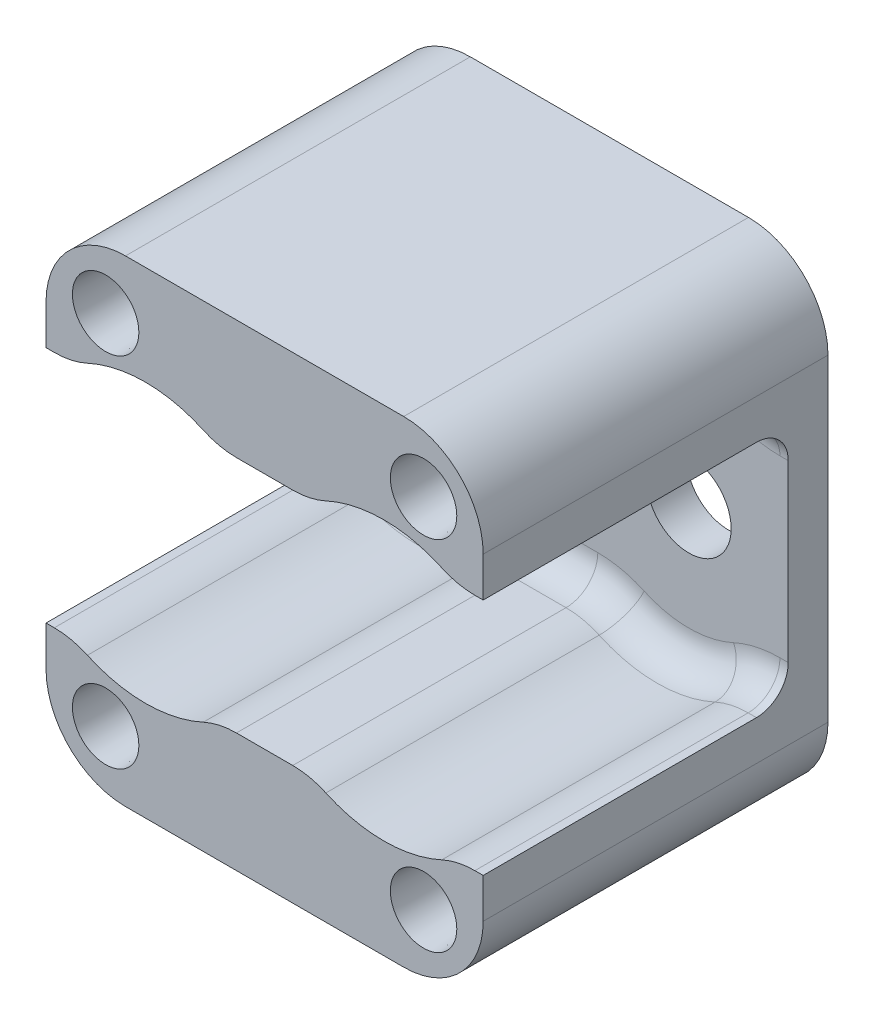
SolidWorks part; units mm, degrees
material "PET"
ref_plane "Front Plane" through (0, 0, 0) normal (0, 0, 1) x (1, 0, 0)
ref_plane "Top Plane" through (0, 0, 0) normal (0, 1, 0) x (1, 0, 0)
ref_plane "Right Plane" through (0, 0, 0) normal (1, 0, 0) x (0, 0, -1)
sketch "Sketch1" plane through (0, 0, 0) normal (0, 0, 1) x (1, 0, 0)
  line L0 (-19.05, 0) -> (0, 0) construction
  line L2 (7.9375, -19.05) -> (-26.9875, -19.05)
  line L3 (7.9375, -19.05) -> (7.9375, 19.05)
  line L4 (7.9375, 19.05) -> (-26.9875, 19.05)
  line L5 (-26.9875, -19.05) -> (-26.9875, 19.05)
  line L6 (7.9375, -19.05) -> (-26.9875, 19.05) construction
  line L7 (7.9375, 19.05) -> (-26.9875, -19.05) construction
  point P4 (-9.525, 0)
  dimension "D1" = 34.925
  dimension "D2" = 38.1
extrude "Boss-Extrude1" add sketch "Sketch1" along normal blind 3.175
sketch "Sketch2" plane through (0, 0, 3.175) normal (0, 0, 1) x (1, 0, 0)
  line L0 (7.9375, -19.05) -> (7.9375, 19.05) construction
  line L1 (-26.9875, 19.05) -> (7.9375, 19.05)
  line L2 (-26.9875, 19.05) -> (-26.9875, 9.525)
  line L3 (-26.9875, 9.525) -> (7.9375, 9.525)
  line L4 (7.9375, 19.05) -> (7.9375, 9.525)
  dimension "D1" = 9.525
extrude "Boss-Extrude2" add sketch "Sketch2" along normal up to surface (24.3713 mm away)
sketch "Sketch3" plane through (0, 0, 19.6088) normal (0, 0, 1) x (1, 0, 0)
  circle A0 centre (-19.05, 0) radius 11.1125
  circle A1 centre (0, 0) radius 11.1125
  dimension "D1" = 22.225
extrude "Cut-Extrude1" cut sketch "Sketch3" against normal up to surface (16.4338 mm away) and the other way through all contours A1 A0 | A0 A1 | A0 A1 up to face at (-13.8906, -4.7625, 3.175)
mirror "Mirror1" about plane through (0, 0, 0) normal (0, 1, 0) of "Cut-Extrude1", "Boss-Extrude2"
fillet "Fillet1" radius 6.35 12 edges at (7.9375, 19.05, 13.7732) (-26.9875, 19.05, 13.7732) (5.7238, 9.525, 15.3607) (-5.7238, 9.525, 15.3607) (-13.3262, 9.525, 15.3607) (-24.7738, 9.525, 15.3607) (7.9375, -19.05, 13.7732) (-26.9875, -19.05, 13.7732) (5.7238, -9.525, 15.3607) (-5.7238, -9.525, 15.3607) (-13.3262, -9.525, 15.3607) (-24.7738, -9.525, 15.3607)
fillet "Fillet2" radius 2.54 18 edges at (5.921, 9.671, 3.175) (0, 11.1125, 3.175) (-5.921, 9.671, 3.175) (-13.129, 9.671, 3.175) (-19.05, 11.1125, 3.175) (-24.971, 9.671, 3.175) (7.6062, -9.525, 3.175) (5.921, -9.671, 3.175) (0, -11.1125, 3.175) (-5.921, -9.671, 3.175) (-9.525, -9.525, 3.175) (-13.129, -9.671, 3.175) (-19.05, -11.1125, 3.175) (-24.971, -9.671, 3.175) (-26.6562, -9.525, 3.175)
sketch "Sketch4" plane through (0, 0, 3.175) normal (0, 0, 1) x (1, 0, 0)
  line L0 (-19.05, 0) -> (-23.3706, 1.7896) construction
  line L1 (-22.5585, -3.2205) -> (-18.8463, -4.7581) construction
  line L2 (-19.8994, 4.7507) -> (-15.0902, 2.7586)
  line L3 (-15.5415, 3.2205) -> (-19.2537, 4.7581) construction
  line L4 (-19.05, 0) -> (-20.8968, -4.4586) construction
  arc A0 (-20.8968, -4.4586) -> (-15.0902, 2.7586) centre (-19.05, 0) ccw
  arc A1 (-19.8994, 4.7507) -> (-20.8968, -4.4586) centre (-19.05, 0) ccw
  dimension "D1" = 9.652
  dimension "D2" = 8.89
extrude "Cut-Extrude2" cut sketch "Sketch4" against normal through all
hole_wizard "1/4 Clearance Hole1" positions "Sketch6" profile "Sketch5" hole size "1/4" standard "ANSI Inch" end condition through all
sketch "Sketch6" plane through (0, 0, 3.175) normal (0, 0, 1) x (1, 0, 0)
  point P0 (0, 0)
sketch "Sketch5" plane through (0, 0, 3.175) normal (1, 0, 0) x (0, -1, 0)
  line L0 (0, 0) -> (0, 3.175)
  line L1 (0, 3.175) -> (3.3782, 3.175)
  line L2 (3.3782, 3.175) -> (3.3782, 0)
  line L5 (3.3782, 0) -> (0, 0)
  line L11 (0, -6.35) -> (0, 107.95) construction
  dimension "Thru Hole Dia." = 6.7564
  dimension "Thru Hole Depth" = 3.175
hole_wizard "#6 Clearance Hole1" positions "Sketch8" profile "Sketch7" hole size "#6" standard "ANSI Inch" end condition through all
sketch "Sketch8" plane through (0, 0, 0) normal (0, 0, -1) x (-1, 0, 0)
  line L0 (-7.9375, -12.7) -> (-7.9375, 12.7) construction
  line L1 (-1.5875, 19.05) -> (20.6375, 19.05) construction
  line L2 (9.525, 19.05) -> (9.525, 0) construction
  line L3 (9.525, 0) -> (26.9875, 0) construction
  line L4 (26.9875, 12.7) -> (26.9875, -12.7) construction
  point P0 (-3.175, 14.2875)
  point P21 (22.225, 14.2875)
  point P23 (22.225, -14.2875)
  point P24 (-3.175, -14.2875)
  dimension "D1" = 4.7625
  dimension "D2" = 4.7625
sketch "Sketch7" plane through (3.175, 14.2875, 0) normal (1, 0, 0) x (0, 1, 0)
  line L0 (0, 0) -> (0, 27.5463)
  line L1 (0, 27.5463) -> (2.1526, 27.5463)
  line L2 (2.1526, 27.5463) -> (2.1526, 0)
  line L5 (2.1526, 0) -> (0, 0)
  line L11 (0, -6.35) -> (0, 107.95) construction
  dimension "Thru Hole Dia." = 4.3053
  dimension "Thru Hole Depth" = 27.5463
hole_wizard "Hole1" positions "Sketch10" profile "Sketch9" legacy
sketch "Sketch10" plane through (0, 0, 27.5463) normal (0, 0, 1) x (1, 0, 0)
  point P0 (-22.225, 14.2875)
  point P3 (3.175, 14.2875)
  point P6 (-22.225, -14.2875)
  point P9 (3.175, -14.2875)
sketch "Sketch9" plane through (-22.225, 14.2875, 27.5463) normal (1, 0, 0) x (0, -1, 0)
  line L0 (0, 0) -> (0, 3.81)
  line L1 (0, 3.81) -> (2.5273, 3.81)
  line L2 (2.5273, 3.81) -> (2.6543, 0)
  line L3 (2.6543, 0) -> (0, 0)
  line L4 (0, 110) -> (0, -10) construction
  dimension "Minor Diameter" = 5.0546
  dimension "Depth" = 3.81
  dimension "Major Diameter" = 5.3086
